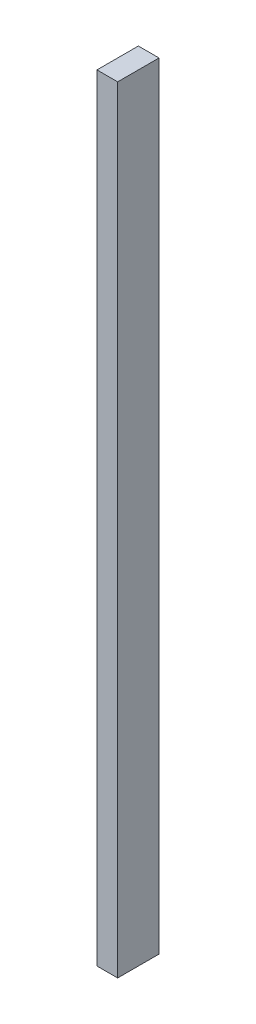
SolidWorks part; units mm, degrees
ref_plane "Front Plane" through (0, 0, 0) normal (0, 0, 1) x (1, 0, 0)
ref_plane "Top Plane" through (0, 0, 0) normal (0, 1, 0) x (1, 0, 0)
ref_plane "Right Plane" through (0, 0, 0) normal (1, 0, 0) x (0, 0, -1)
sketch "Sketch1" plane through (0, 0, 0) normal (0, 0, 1) x (1, 0, 0)
  line L1 (0, 0) -> (-0.8, 0)
  line L2 (0, 0) -> (0, 30)
  line L3 (0, 30) -> (-0.8, 30)
  line L4 (-0.8, 0) -> (-0.8, 30)
  dimension "D1" = 0.8
  dimension "D2" = 30
  dimension "D3" = 0
  dimension "D4" = 0
extrude "Boss-Extrude1" add sketch "Sketch1" along normal blind 1.6
